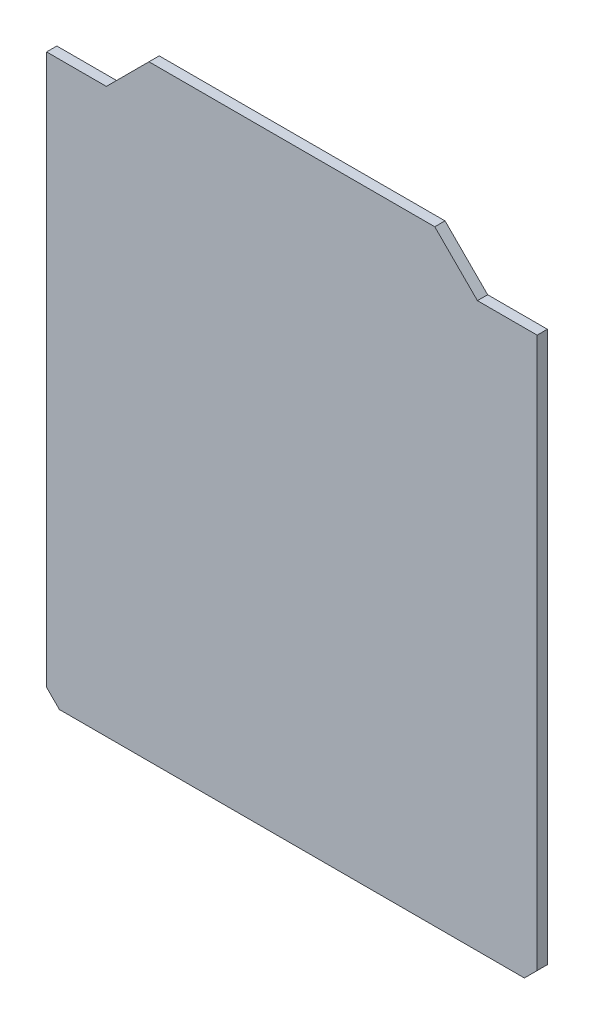
SolidWorks part; units mm, degrees
ref_plane "前视基准面" through (0, 0, 0) normal (0, 0, 1) x (1, 0, 0)
ref_plane "上视基准面" through (0, 0, 0) normal (0, 1, 0) x (1, 0, 0)
ref_plane "右视基准面" through (0, 0, 0) normal (1, 0, 0) x (0, 0, -1)
sketch "草图1" plane through (0, 0, 0) normal (0, 0, 1) x (1, 0, 0)
  line L0 (-21.2996, 40.5934) -> (-16.2996, 45.5934)
  line L1 (-28.2996, 40.5934) -> (29.2004, 40.5934) construction
  line L2 (-28.2996, 40.5934) -> (-28.2996, -25.4144)
  line L3 (-28.2996, -25.4144) -> (29.2004, -25.4144)
  line L4 (29.2004, 40.5934) -> (29.2004, -25.4144)
  line L5 (17.2004, 45.5934) -> (22.2004, 40.5934)
  line L6 (17.2004, 45.5934) -> (-16.2996, 45.5934)
  line L7 (-28.2996, 40.5934) -> (-21.2996, 40.5934)
  line L8 (22.2004, 40.5934) -> (29.2004, 40.5934)
  point P1 (0, 0)
  dimension "D1" = 57.5
  dimension "D2" = 45
  dimension "D3" = 5
  dimension "D4" = 7
extrude "凸台-拉伸1" add sketch "草图1" along normal blind 1.2
chamfer "倒角1" distance 1.5 angle 45 2 edges at (-28.2996, -25.4144, 0.6) (29.2004, -25.4144, 0.6)
